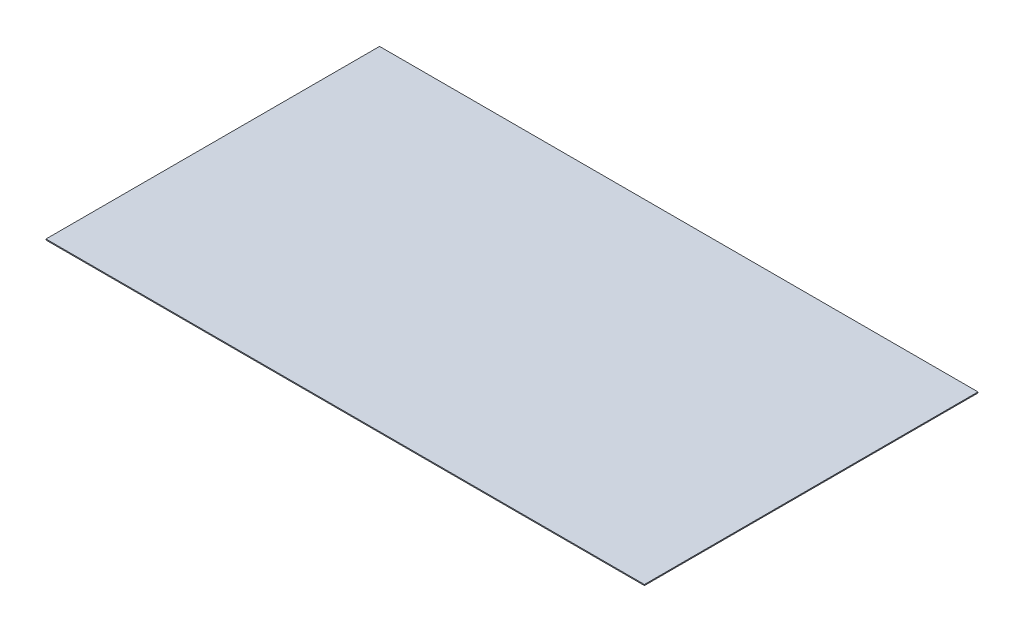
SolidWorks part; units mm, degrees
ref_plane "Face" through (0, 0, 0) normal (0, 0, 1) x (1, 0, 0)
ref_plane "Dessus" through (0, 0, 0) normal (0, 1, 0) x (1, 0, 0)
ref_plane "Droite" through (0, 0, 0) normal (1, 0, 0) x (0, 0, -1)
sketch "Esquisse1" plane through (0, 0, 0) normal (0, 1, 0) x (1, 0, 0)
  line L1 (0, 0) -> (610, 0)
  line L2 (0, 0) -> (0, 340)
  line L3 (0, 340) -> (610, 340)
  line L4 (610, 0) -> (610, 340)
  dimension "D1" = 610
  dimension "D2" = 340
extrude "Extrusion1" add sketch "Esquisse1" along normal blind 1
